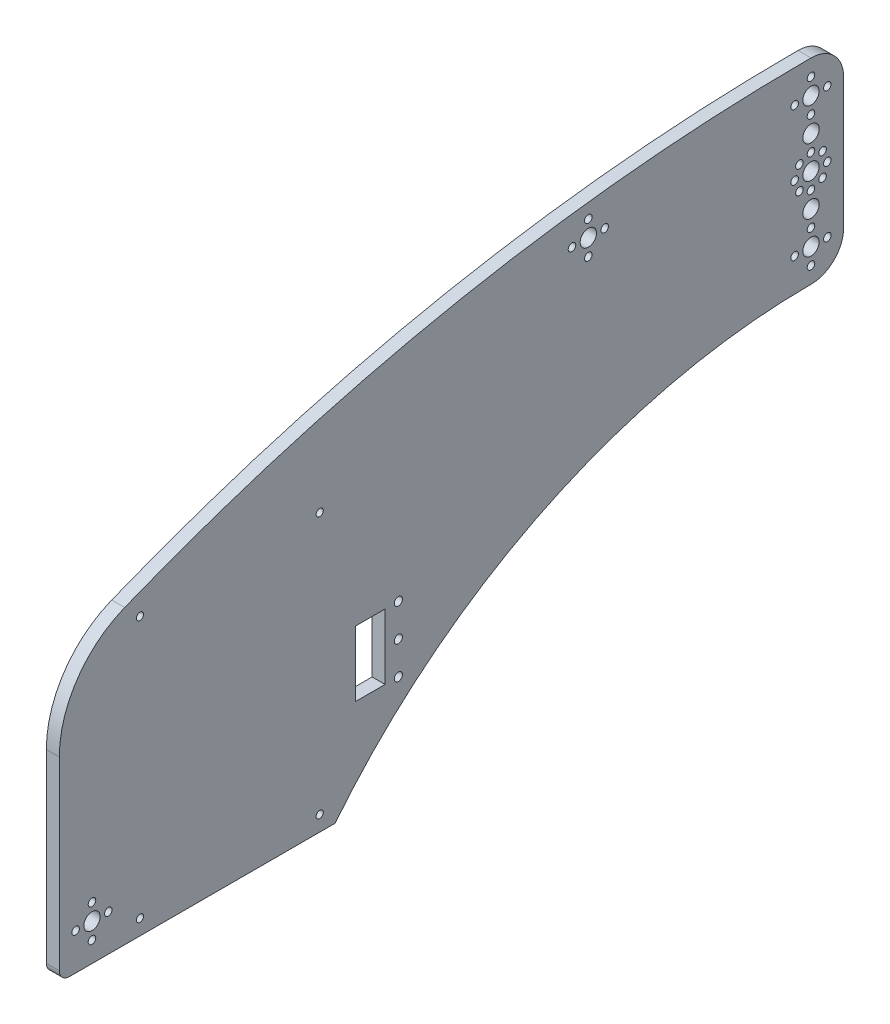
SolidWorks part; units mm, degrees
ref_plane "Front Plane" through (0, 0, 0) normal (0, 0, 1) x (1, 0, 0)
ref_plane "Top Plane" through (0, 0, 0) normal (0, 1, 0) x (1, 0, 0)
ref_plane "Right Plane" through (0, 0, 0) normal (1, 0, 0) x (0, 0, -1)
sketch "Sketch1" plane through (0, 0, 0) normal (1, 0, 0) x (0, 0, -1)
  line L0 (352, 110) -> (352, 126) construction
  line L1 (352, 110) -> (352, 118) construction
  line L2 (335.394, 142) -> (383.5261, 142) construction
  line L3 (352, 174) -> (352, 166) construction
  line L4 (352, 174) -> (352, 158) construction
  line L5 (-16, -18) -> (16, -18) construction
  line L6 (16, -18) -> (16, -50) construction
  line L7 (16, -50) -> (-16, -50) construction
  line L8 (-16, 77.6494) -> (-16, -13)
  line L9 (-11, -18) -> (119, -18)
  line L10 (368, 174) -> (368, 110)
  line L19 (129, 28.6253) -> (143.5, 28.6253)
  line L20 (129, 28.6253) -> (129, 60.6253)
  line L21 (143.5, 28.6253) -> (143.5, 60.6253)
  line L22 (129, 60.6253) -> (143.5, 60.6253)
  line L23 (150, 28.6253) -> (150, 60.6253) construction
  circle A0 centre (352, 110) radius 4
  circle A1 centre (352, 118) radius 1.85
  circle A2 centre (352, 126) radius 4
  circle A3 centre (352, 134) radius 1.85
  circle A4 centre (352, 142) radius 4
  circle A6 centre (352, 150) radius 1.85 [skipped]
  circle A7 centre (360, 110) radius 1.85
  circle A8 centre (352, 102) radius 1.85
  circle A9 centre (344, 110) radius 1.85
  circle A10 centre (346.3431, 136.3431) radius 1.85
  circle A11 centre (344, 142) radius 1.85
  circle A12 centre (346.3431, 147.6569) radius 1.85
  circle A13 centre (352, 150) radius 1.85
  circle A14 centre (357.6569, 147.6569) radius 1.85
  circle A15 centre (360, 142) radius 1.85
  circle A16 centre (357.6569, 136.3431) radius 1.85
  circle A17 centre (344, 174) radius 1.85
  circle A18 centre (352, 182) radius 1.85
  circle A19 centre (360, 174) radius 1.85
  circle A20 centre (352, 158) radius 4
  circle A21 centre (352, 166) radius 1.85
  circle A22 centre (352, 174) radius 4
  arc A23 (16, 125) -> (352, 190) centre (352, -710.9308) cw
  arc A24 (-16, -13) -> (-11, -18) centre (-11, -13) ccw
  arc A25 (352, 94) -> (119, -18) centre (352, -204.3616) ccw
  arc A26 (352, 190) -> (368, 174) centre (352, 174) cw
  arc A27 (368, 110) -> (352, 94) centre (352, 110) cw
  circle A28 centre (0, 0) radius 4
  circle A29 centre (8, 0) radius 1.85
  circle A30 centre (0, -8) radius 1.85
  circle A31 centre (-8, 0) radius 1.85
  circle A32 centre (0, 8) radius 1.85
  arc A37 (16, 125) -> (-16, 77.6494) centre (35.0324, 77.6494) ccw
  circle A38 centre (150, 28.6253) radius 2
  circle A39 centre (150, 44.6253) radius 2
  circle A40 centre (150, 60.6253) radius 2
  circle A41 centre (243, 168.2691) radius 4
  circle A42 centre (251, 168.2691) radius 1.85
  circle A43 centre (243, 160.2691) radius 1.85
  circle A44 centre (235, 168.2691) radius 1.85
  circle A45 centre (243, 176.2691) radius 1.85
  point P25 (352, 142)
  point P38 (352, 142)
  point P70 (0, -50)
  point P79 (0, 0)
  point P113 (243, 168.2691)
  line B0 (23.5, 117.5) -> (23.5, -10.5) construction
  line B1 (16, 125) -> (119, 125) construction
  line B2 (16, 125) -> (16, -18) construction
  line B3 (16, -18) -> (119, -18) construction
  line B4 (119, 125) -> (119, -18) construction
  line B5 (23.5, -10.5) -> (111.5, -10.5) construction
  line B6 (111.5, 117.5) -> (111.5, -10.5) construction
  line B7 (23.5, 117.5) -> (111.5, 117.5) construction
  circle B8 centre (23.5, 117.5) radius 1.75
  circle B9 centre (111.5, 117.5) radius 1.75
  circle B10 centre (111.5, -10.5) radius 1.75
  circle B11 centre (23.5, -10.5) radius 1.75
  dimension "D1" = 8
  dimension "D2" = 3.7
  dimension "D12" = 5
  dimension "D18" = 8
  dimension "D19" = 3.7
  dimension "D14" = 16
  dimension "D25" = 4
  dimension "D28" = 10
  dimension "D29" = 10
  dimension "D30" = 8
  dimension "D31" = 3.7
  dimension "D3" = 8
  dimension "D5" = 16
  dimension "D7" = 8
  dimension "D8" = 32
  dimension "D9" = 336
  dimension "D10" = 160
  dimension "D11" = 16
  dimension "D13" = 16
  dimension "D15" = 16
  dimension "D16" = 18
  dimension "D17" = 8
  dimension "D26" = 6.5
  dimension "D27" = 14.5
  dimension "D32" = 8
  dimension "D34" = 15
  dimension "D35" = 125
  dimension "D4" = 3
  dimension "D6" = 4
  dimension "D20" = 4
  dimension "D33" = 4
sketch_block_instance "Block1-1"
sketch_block "Block1" parameters "D1"=3.5, "D2"=143, "D3"=103
extrude "Boss-Extrude2" add sketch "Sketch1" along normal blind 6.35
